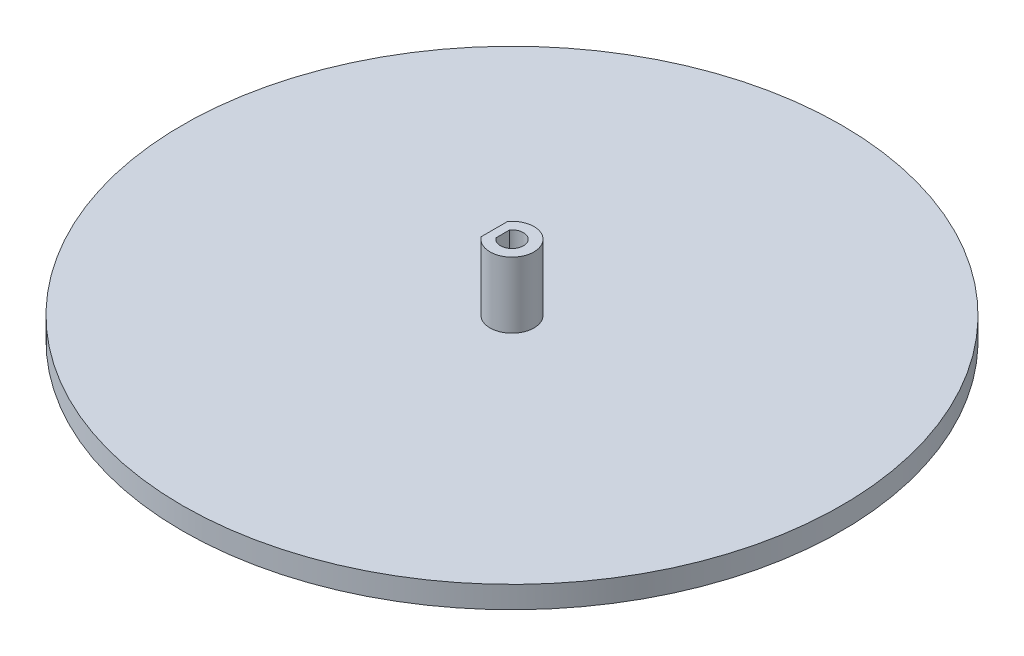
SolidWorks part; units mm, degrees
ref_plane "Front Plane" through (0, 0, 0) normal (0, 0, 1) x (1, 0, 0)
ref_plane "Top Plane" through (0, 0, 0) normal (0, 1, 0) x (1, 0, 0)
ref_plane "Right Plane" through (0, 0, 0) normal (1, 0, 0) x (0, 0, -1)
sketch "Sketch1" plane through (0, 0, 0) normal (0, 1, 0) x (1, 0, 0)
  circle A0 centre (0, 0) radius 75
  dimension "D1" = 150
extrude "Boss-Extrude1" add sketch "Sketch1" along normal blind 5
sketch "Sketch3" plane through (0, 5, 0) normal (0, 1, 0) x (1, 0, 0)
  line L0 (-2.1, 1.533) -> (-2.1, -1.533)
  line L1 (-4, 3) -> (-4, -3)
  arc A0 (-2.1, -1.533) -> (-2.1, 1.533) centre (0, 0) ccw
  arc A1 (-4, -3) -> (-4, 3) centre (0, 0) ccw
  dimension "D1" = 5.2
  dimension "D3" = 10
  dimension "D2" = 2.1
  dimension "D4" = 4
extrude "Boss-Extrude2" add sketch "Sketch3" along normal blind 15
